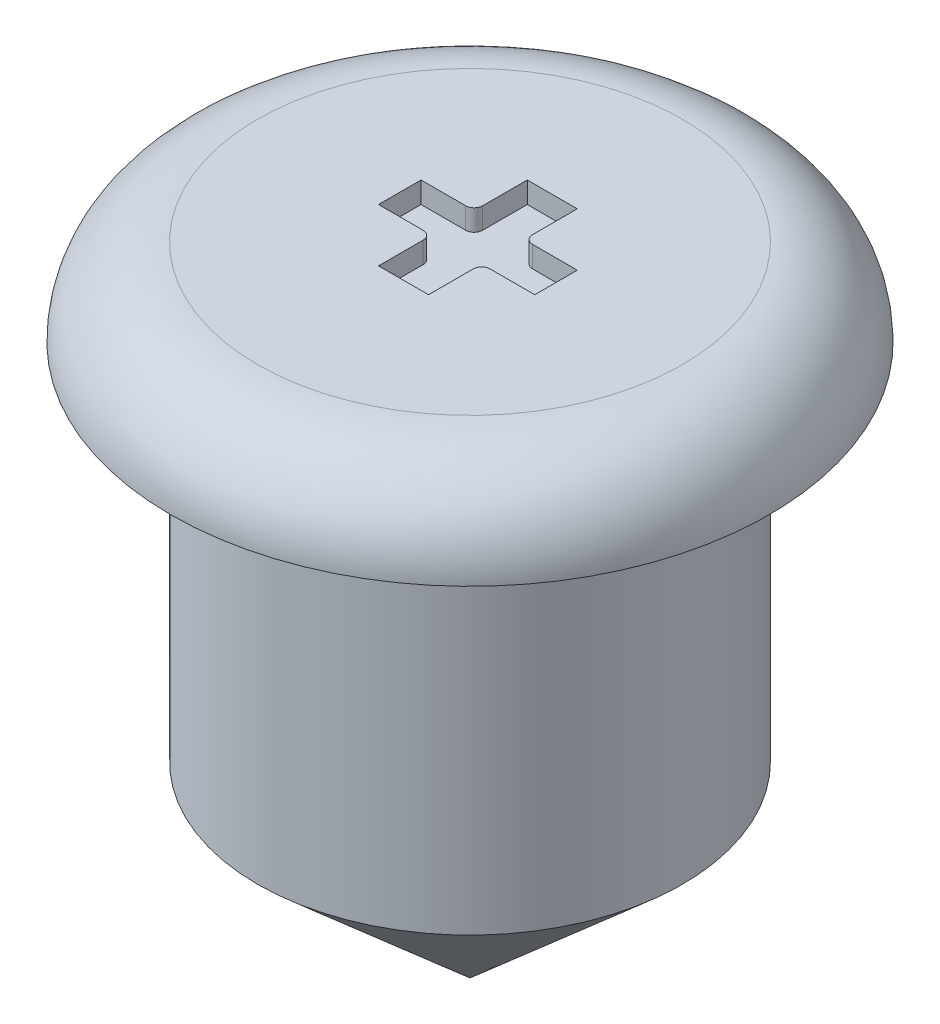
SolidWorks part; units mm, degrees
ref_plane "Front" through (0, 0, 0) normal (0, 0, 1) x (1, 0, 0)
ref_plane "Top" through (0, 0, 0) normal (0, 1, 0) x (1, 0, 0)
ref_plane "Right" through (0, 0, 0) normal (1, 0, 0) x (0, 0, -1)
sketch "Sketch1" plane through (0, 0, 0) normal (0, 0, 1) x (1, 0, 0)
  line L1 (0, -55) -> (0, 55) construction
  line L2 (1, -15.0181) -> (1, -13.308)
  line L3 (1.4081, -13.308) -> (1, -13.308)
  line L4 (1, -12.8999) -> (0, -12.8999)
  line L5 (0, -12.8999) -> (0, -15.8999)
  line L6 (0, -15.8999) -> (1, -15.0181)
  arc A0 (1.4081, -13.308) -> (1, -12.8999) centre (1, -13.308) ccw
  point P7 (1, -12.8999)
revolve "Revolve1" add sketch "Sketch1" angle 360 about L5
cosmetic thread "Cosmetic Thread1" parameters "D2"=0.911
sketch "Sketch2" plane through (0, -12.8999, 0) normal (0, 1, 0) x (1, 0, 0)
  line L0 (-0.1176, 0.3872) -> (0.1176, 0.3872)
  line L1 (0.1176, 0.3872) -> (0.1176, 0.1772)
  line L2 (0.1576, 0.1372) -> (0.3676, 0.1372)
  line L3 (0.3676, 0.1372) -> (0.3676, -0.0628)
  line L4 (0.3676, -0.0628) -> (0.1576, -0.0628)
  line L5 (0.1176, -0.1028) -> (0.1176, -0.3128)
  line L6 (0.1176, -0.3128) -> (-0.1176, -0.3128)
  line L7 (0, 0.3872) -> (0, -0.3128) construction
  line L8 (-0.1176, -0.1028) -> (-0.1176, -0.3128)
  line L9 (-0.3676, -0.0628) -> (-0.1576, -0.0628)
  line L10 (-0.3676, 0.1372) -> (-0.3676, -0.0628)
  line L11 (-0.1576, 0.1372) -> (-0.3676, 0.1372)
  line L12 (-0.1176, 0.3872) -> (-0.1176, 0.1772)
  line L13 (0, -1.5489) -> (0, 1.5489) construction
  arc A0 (0.1176, 0.1772) -> (0.1576, 0.1372) centre (0.1576, 0.1772) ccw
  arc A1 (0.1576, -0.0628) -> (0.1176, -0.1028) centre (0.1576, -0.1028) ccw
  arc A2 (-0.1576, -0.0628) -> (-0.1176, -0.1028) centre (-0.1576, -0.1028) cw
  arc A3 (-0.1176, 0.1772) -> (-0.1576, 0.1372) centre (-0.1576, 0.1772) cw
  dimension "D1" = 0.04
  dimension "D2" = 0.04
extrude "Cut-Extrude1" cut sketch "Sketch2" against normal blind 0.1
